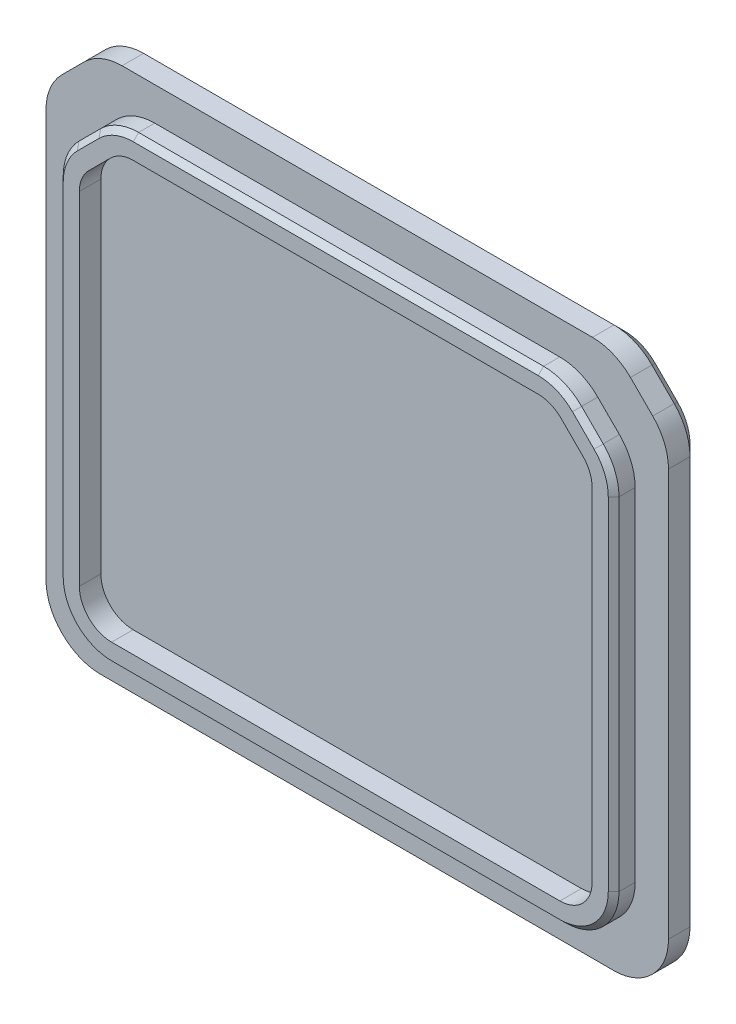
SolidWorks part; units mm, degrees
ref_plane "Front Plane" through (0, 0, 0) normal (0, 0, 1) x (1, 0, 0)
ref_plane "Top Plane" through (0, 0, 0) normal (0, 1, 0) x (1, 0, 0)
ref_plane "Right Plane" through (0, 0, 0) normal (1, 0, 0) x (0, 0, -1)
sketch "Sketch2" plane through (0, 0, -23.3905) normal (0, 0, -1) x (-1, 0, 0)
  line L16 (21.4289, 26) -> (-22.3079, 26)
  line L18 (-29.379, 18.9289) -> (-29.379, -18.9289)
  line L20 (-24.3079, -24) -> (23.4289, -24)
  line L22 (28.5, -18.9289) -> (28.5, 18.9289)
  line L24 (21.4289, 26) -> (-22.3079, 26)
  line L26 (-29.379, 18.9289) -> (-29.379, -18.9289)
  line L28 (-24.3079, -24) -> (23.4289, -24)
  line L30 (28.5, -18.9289) -> (28.5, 18.9289)
  line L60 (-25.8435, 24.5355) -> (-27.9145, 22.4645)
  line L61 (-25.8435, 24.5355) -> (-27.9145, 22.4645)
  line L62 (-27.9145, -22.4645) -> (-27.8435, -22.5355)
  line L63 (-27.9145, -22.4645) -> (-27.8435, -22.5355)
  line L64 (26.9645, -22.5355) -> (27.0355, -22.4645)
  line L65 (26.9645, -22.5355) -> (27.0355, -22.4645)
  line L66 (27.0355, 22.4645) -> (24.9645, 24.5355)
  line L67 (27.0355, 22.4645) -> (24.9645, 24.5355)
  arc A52 (-22.3079, 26) -> (-25.8435, 24.5355) centre (-22.3079, 21) ccw
  arc A53 (-22.3079, 26) -> (-25.8435, 24.5355) centre (-22.3079, 21) ccw
  arc A54 (-27.9145, 22.4645) -> (-29.379, 18.9289) centre (-24.379, 18.9289) ccw
  arc A55 (-27.9145, 22.4645) -> (-29.379, 18.9289) centre (-24.379, 18.9289) ccw
  arc A56 (-29.379, -18.9289) -> (-27.9145, -22.4645) centre (-24.379, -18.9289) ccw
  arc A57 (-29.379, -18.9289) -> (-27.9145, -22.4645) centre (-24.379, -18.9289) ccw
  arc A58 (-27.8435, -22.5355) -> (-24.3079, -24) centre (-24.3079, -19) ccw
  arc A59 (-27.8435, -22.5355) -> (-24.3079, -24) centre (-24.3079, -19) ccw
  arc A60 (23.4289, -24) -> (26.9645, -22.5355) centre (23.4289, -19) ccw
  arc A61 (23.4289, -24) -> (26.9645, -22.5355) centre (23.4289, -19) ccw
  arc A62 (27.0355, -22.4645) -> (28.5, -18.9289) centre (23.5, -18.9289) ccw
  arc A63 (27.0355, -22.4645) -> (28.5, -18.9289) centre (23.5, -18.9289) ccw
  arc A64 (28.5, 18.9289) -> (27.0355, 22.4645) centre (23.5, 18.9289) ccw
  arc A65 (28.5, 18.9289) -> (27.0355, 22.4645) centre (23.5, 18.9289) ccw
  arc A66 (24.9645, 24.5355) -> (21.4289, 26) centre (21.4289, 21) ccw
  arc A67 (24.9645, 24.5355) -> (21.4289, 26) centre (21.4289, 21) ccw
  dimension "D1" = 0
extrude "Boss-Extrude1" add sketch "Sketch2" along normal blind 3
sketch "Sketch3" plane through (0, 0, -23.3905) normal (0, 0, -1) x (-1, 0, 0)
  line L16 (-24.279, -18.9) -> (23.4, -18.9)
  line L17 (23.4, -18.9) -> (23.4, 17.1302)
  line L18 (23.4, 17.1302) -> (19.6302, 20.9)
  line L19 (19.6302, 20.9) -> (-20.5092, 20.9)
  line L20 (-20.5092, 20.9) -> (-24.279, 17.1302)
  line L21 (-24.279, 17.1302) -> (-24.279, -18.9)
  line L100 (-26.279, -20.9) -> (25.4, -20.9)
  line L101 (25.4, -20.9) -> (25.4, 17.9586)
  line L102 (-26.279, 17.9586) -> (-26.279, -20.9)
  line L103 (20.4586, 22.9) -> (-21.3376, 22.9)
  line L104 (25.4, 17.9586) -> (20.4586, 22.9)
  line L105 (-21.3376, 22.9) -> (-26.279, 17.9586)
  line L106 (-26.279, -20.9) -> (25.4, -20.9)
  line L107 (25.4, -20.9) -> (25.4, 17.9586)
  line L108 (-26.279, 17.9586) -> (-26.279, -20.9)
  line L109 (20.4586, 22.9) -> (-21.3376, 22.9)
  line L110 (25.4, 17.9586) -> (20.4586, 22.9)
  line L111 (-21.3376, 22.9) -> (-26.279, 17.9586)
  dimension "D1" = 2
  dimension "D2" = 0.1
extrude "Boss-Extrude2" add sketch "Sketch3" against normal blind 2
chamfer "Chamfer1" distance 1 angle 45 16 edges at (-26, 23.5, -26.3905) (-28.1194, 20.8423, -26.3905) (-28.5, 0, -26.3905) (-28.1194, -20.8423, -26.3905) (-27, -22.5, -26.3905) (-25.3423, -23.6194, -26.3905) (0.4395, -24, -26.3905) (26.2213, -23.6194, -26.3905) (27.879, -22.5, -26.3905) (28.9984, -20.8423, -26.3905) (29.379, 0, -26.3905) (28.9984, 20.8423, -26.3905) (26.879, 23.5, -26.3905) (24.2213, 25.6194, -26.3905) (0.4395, 26, -26.3905) (-23.3423, 25.6194, -26.3905)
fillet "Fillet1" radius 3 6 edges at (-19.6302, 20.9, -22.3905) (-23.4, 17.1302, -22.3905) (24.279, 17.1302, -22.3905) (20.5092, 20.9, -22.3905) (24.279, -18.9, -22.3905) (-23.4, -18.9, -22.3905)
fillet "Fillet2" radius 5 6 edges at (-25.4, 17.9586, -22.3905) (-20.4586, 22.9, -22.3905) (21.3376, 22.9, -22.3905) (26.279, 17.9586, -22.3905) (-25.4, -20.9, -22.3905) (26.279, -20.9, -22.3905)
chamfer "Chamfer2" distance 0.5 angle 45 12 edges at (23.8083, 20.4293, -21.3905) (25.8984, 17.8009, -21.3905) (21.1799, 22.5194, -21.3905) (26.279, -0.0062, -21.3905) (0.4395, 22.9, -21.3905) (24.8145, -19.4355, -21.3905) (-20.3009, 22.5194, -21.3905) (0.4395, -20.9, -21.3905) (-22.9293, 20.4293, -21.3905) (-23.9355, -19.4355, -21.3905) (-25.0194, 17.8009, -21.3905) (-25.4, -0.0062, -21.3905)
